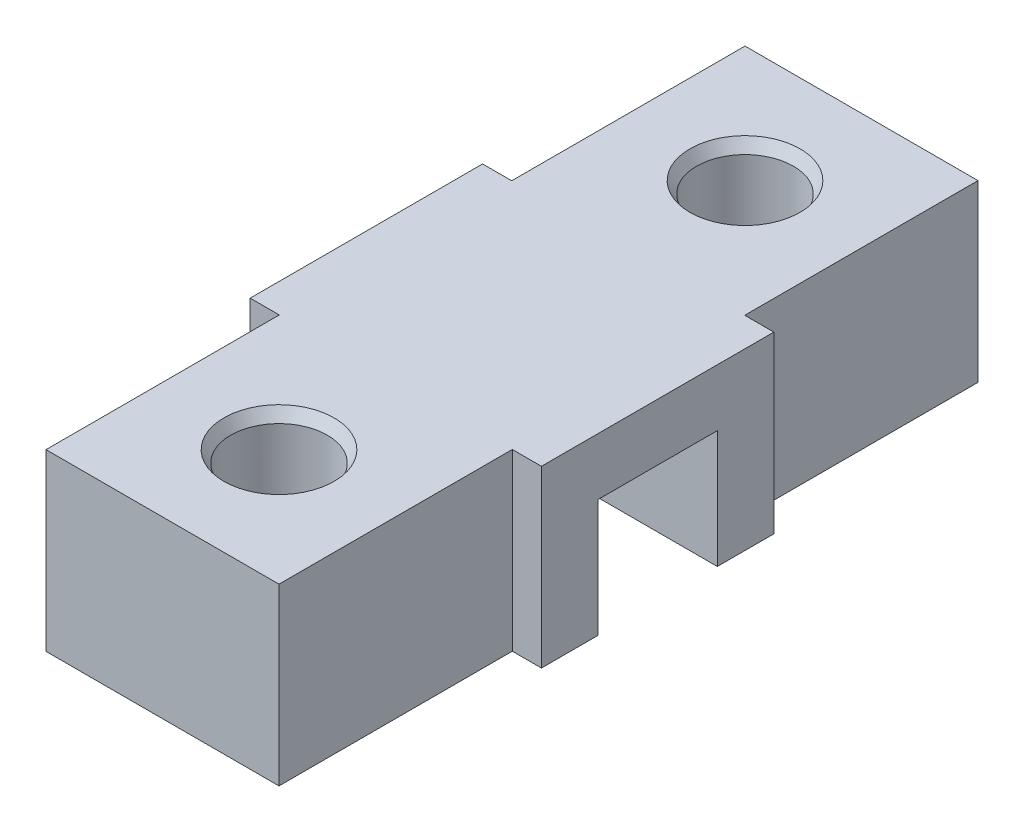
SolidWorks part; units mm, degrees
ref_plane "Спереди" through (0, 0, 0) normal (0, 0, 1) x (1, 0, 0)
ref_plane "Сверху" through (0, 0, 0) normal (0, 1, 0) x (1, 0, 0)
ref_plane "Справа" through (0, 0, 0) normal (1, 0, 0) x (0, 0, -1)
sketch "Sketch1" plane through (0, 0, 0) normal (0, 1, 0) x (1, 0, 0)
  line L1 (10, -30) -> (-10, -30)
  line L2 (10, -30) -> (10, 30)
  line L3 (10, 30) -> (-10, 30)
  line L4 (-10, -30) -> (-10, 30)
  line L5 (10, -30) -> (-10, 30) construction
  line L6 (10, 30) -> (-10, -30) construction
  point P0 (0, 0)
  dimension "D1" = 20
  dimension "D2" = 60
extrude "Boss-Extrude1" add sketch "Sketch1" along normal blind 15
sketch "Sketch2" plane through (10, 0, 0) normal (1, 0, 0) x (0, 0, -1)
  line L0 (0, 0) -> (0, 15) construction
  line L1 (-30, 0) -> (30, 0) construction
  line L2 (-30, 15) -> (30, 15) construction
  line L4 (5.125, 10.1) -> (-5.125, 10.1)
  line L5 (5.125, 10.1) -> (5.125, 0)
  line L6 (5.125, 0) -> (-5.125, 0)
  line L7 (-5.125, 10.1) -> (-5.125, 0)
  line L8 (5.125, 10.1) -> (-5.125, 0) construction
  line L9 (5.125, 0) -> (-5.125, 10.1) construction
  point P6 (0, 5.05)
  dimension "D1" = 10.25
  dimension "D2" = 10.1
extrude "Cut-Extrude1" cut sketch "Sketch2" against normal through all and the other way through all
sketch "Sketch3" plane through (0, 0, 0) normal (0, -1, 0) x (1, 0, 0)
  line L0 (0, 30) -> (0, -30) construction
  line L1 (-10, 30) -> (10, 30) construction
  line L2 (10, -30) -> (-10, -30) construction
  circle A0 centre (0, 20) radius 4.15
  circle A1 centre (0, -20) radius 4.15
  dimension "D1" = 8.3
  dimension "D2" = 20
  dimension "D3" = 40
extrude "Cut-Extrude2" cut sketch "Sketch3" against normal through all
sketch "Sketch4" plane through (10, 0, 0) normal (1, 0, 0) x (0, 0, -1)
  line L0 (-5.125, 0) -> (-9.975, 0)
  line L1 (-30, 0) -> (-5.125, 0) construction
  line L2 (-9.975, 0) -> (-9.975, 15)
  line L3 (-30, 15) -> (30, 15) construction
  line L4 (-9.975, 15) -> (9.975, 15)
  line L5 (9.975, 15) -> (9.975, 0)
  line L6 (5.125, 0) -> (30, 0) construction
  line L7 (9.975, 0) -> (5.125, 0)
  line L8 (5.125, 0) -> (5.125, 10.1)
  line L9 (5.125, 10.1) -> (-5.125, 10.1)
  line L10 (-5.125, 10.1) -> (-5.125, 0)
  dimension "D1" = 4.85
extrude "Boss-Extrude2" add sketch "Sketch4" along normal blind 2.5 and the other way blind 22.5
chamfer "Chamfer1" distance 1 angle 30 2 edges at (0, 15, -24.15) (0, 15, 15.85)
